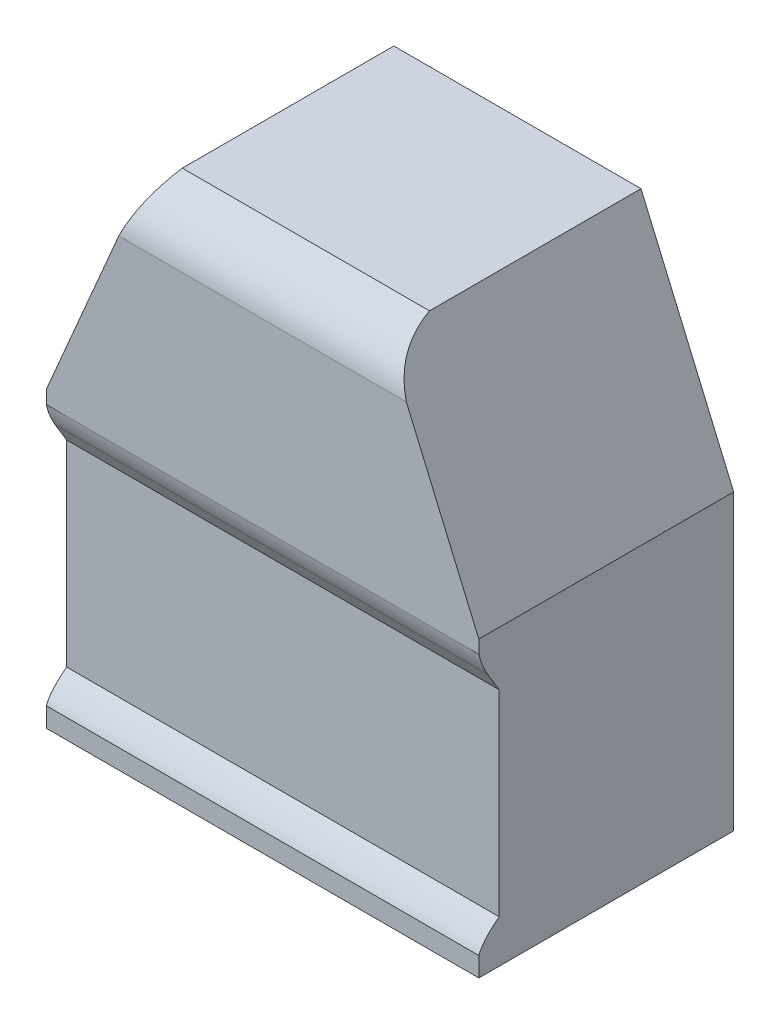
SolidWorks part; units mm, degrees
ref_plane "Front Plane" through (0, 0, 0) normal (0, 0, 1) x (1, 0, 0)
ref_plane "Top Plane" through (0, 0, 0) normal (0, 1, 0) x (1, 0, 0)
ref_plane "Right Plane" through (0, 0, 0) normal (1, 0, 0) x (0, 0, -1)
sketch "Sketch1" plane through (0, 0, 0) normal (0, 0, 1) x (1, 0, 0)
  line L0 (0, 0) -> (0, 235) construction
  line L2 (-140, 95) -> (-140, -95)
  line L3 (-140, -95) -> (140, -95)
  line L4 (140, 95) -> (140, -95)
  line L5 (-140, 95) -> (140, -95) construction
  line L6 (-140, -95) -> (140, 95) construction
  line L7 (80, 235) -> (-80, 235)
  line L8 (-140, 95) -> (-80, 235)
  line L9 (80, 235) -> (140, 95)
  point P1 (0, 0)
  point P11 (0, 235)
  dimension "D1" = 280
  dimension "D2" = 160
  dimension "D4" = 190
extrude "Boss-Extrude1" add sketch "Sketch1" along normal blind 100 and the other way blind 65
sketch "Sketch2" plane through (140, 0, 0) normal (1, 0, 0) x (0, 0, -1)
  line L0 (65, 235) -> (-100, 235) construction
  line L1 (-100, 95) -> (-100, 235) construction
  line L2 (-100, 190.3772) -> (-100, 104.5137)
  line L3 (-100, -95) -> (-100, 95) construction
  line L4 (-94.3842, 72.5254) -> (-86.8621, 60.0814)
  line L5 (-86.8621, 60.0814) -> (-86.8621, -67.2131)
  line L6 (-71.9363, 235) -> (-158.3609, 235)
  line L7 (-158.3609, 235) -> (-158.3609, -95)
  line L8 (-158.3609, -95) -> (-100, -95)
  spline S0 degree 2 poles (-71.9363, 235) (-104.0524, 224.516) (-100, 190.3772) knots 0 0 0 1 1 1
  spline S1 degree 3 poles (-100, 104.5137) (-102.2245, 93.0616) (-100.3526, 82.3988) (-94.3842, 72.5254) knots 0 0 0 0 1 1 1 1
  spline S2 degree 3 poles (-86.8621, -67.2131) (-95.0402, -73.5632) (-104.8104, -83.1012) (-100, -95) knots 0 0 0 0 1 1 1 1
extrude "Cut-Extrude1" cut sketch "Sketch2" against normal blind 280
sketch "Sketch3" plane through (0, 0, 100) normal (0, 0, 1) x (1, 0, 0)
  line L0 (0, 0) -> (0, 247.0582) construction
  line L1 (-37.5, 234.9003) -> (37.5, 235)
  line L4 (-25, 162.8784) -> (25, 162.8784)
  line L8 (-80, 235) -> (80, 235) construction
  line L9 (37.5, 235) -> (25, 162.8784)
  line L10 (-37.5, 234.9003) -> (-25, 162.8784)
  point P3 (0, 204.4071)
  point P13 (0, 234.9502)
  dimension "D1" = 50
  dimension "D2" = 75
